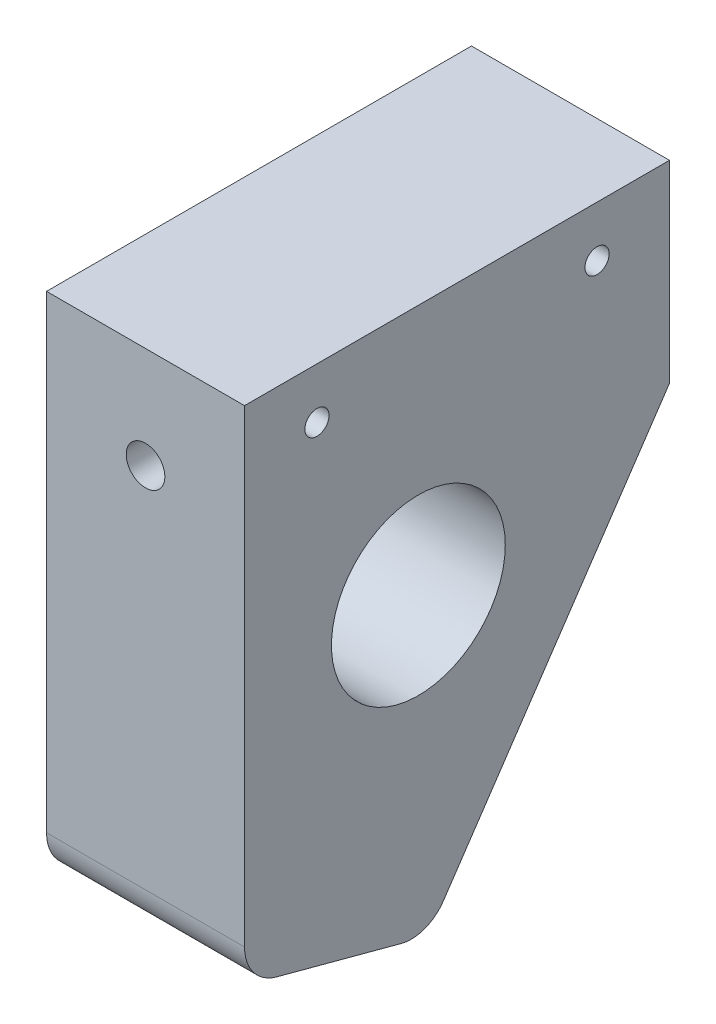
SolidWorks part; units mm, degrees
ref_plane "前基準面" through (0, 0, 0) normal (0, 0, 1) x (1, 0, 0)
ref_plane "上基準面" through (0, 0, 0) normal (0, 1, 0) x (1, 0, 0)
ref_plane "右基準面" through (0, 0, 0) normal (1, 0, 0) x (0, 0, -1)
sketch "草圖1" plane through (0, 0, 0) normal (1, 0, 0) x (0, 0, -1)
  line L0 (-390.8654, 429.7867) -> (72.9461, 893.5982) construction
  line L1 (-44, 0) -> (-44, -48.547)
  line L2 (0, 0) -> (0, -20)
  line L3 (-44, 0) -> (0, 0)
  line L4 (-27.7714, -56.3484) -> (-40.6647, -52.8937)
  line L5 (0, -20) -> (-23.42, -54.7215)
  line L6 (-22, -11.5446) -> (-22, 11.5446) construction
  arc A0 (-44, -48.547) -> (-40.6647, -52.8937) centre (-39.5, -48.547) ccw
  arc A1 (-27.7714, -56.3484) -> (-23.42, -54.7215) centre (-26.7361, -52.4847) ccw
  circle A2 centre (-26, -26) radius 9
  circle A3 centre (-36.5, -5.25) radius 1.25
  circle A4 centre (-7.5, -5.25) radius 1.25
  point P15 (-44, -52)
  point P23 (-22, 0)
  dimension "D6" = 4.5
  dimension "D7" = 4
  dimension "D8" = 18
  dimension "D11" = 2.5
  dimension "D12" = 29
  dimension "D1" = 44
  dimension "D2" = 20
  dimension "D3" = 105
  dimension "D4" = 109
  dimension "D5" = 52
  dimension "D9" = 26
  dimension "D10" = 18
  dimension "D13" = 5.25
extrude "填料-伸長1" add sketch "草圖1" along normal mid plane 20.5
sketch "草圖2" plane through (0, 0, 44) normal (0, 0, 1) x (1, 0, 0)
  line L0 (0, -9.0725) -> (0, 9.0725) construction
  line L1 (10.25, 0) -> (-10.25, 0) construction
  circle A0 centre (0, -10.5) radius 2
  point P3 (0, -11.8453)
  point P6 (0, 0)
  dimension "D1" = 10.5
  dimension "D2" = 4
extrude "除料-伸長1" cut sketch "草圖2" against normal through all
